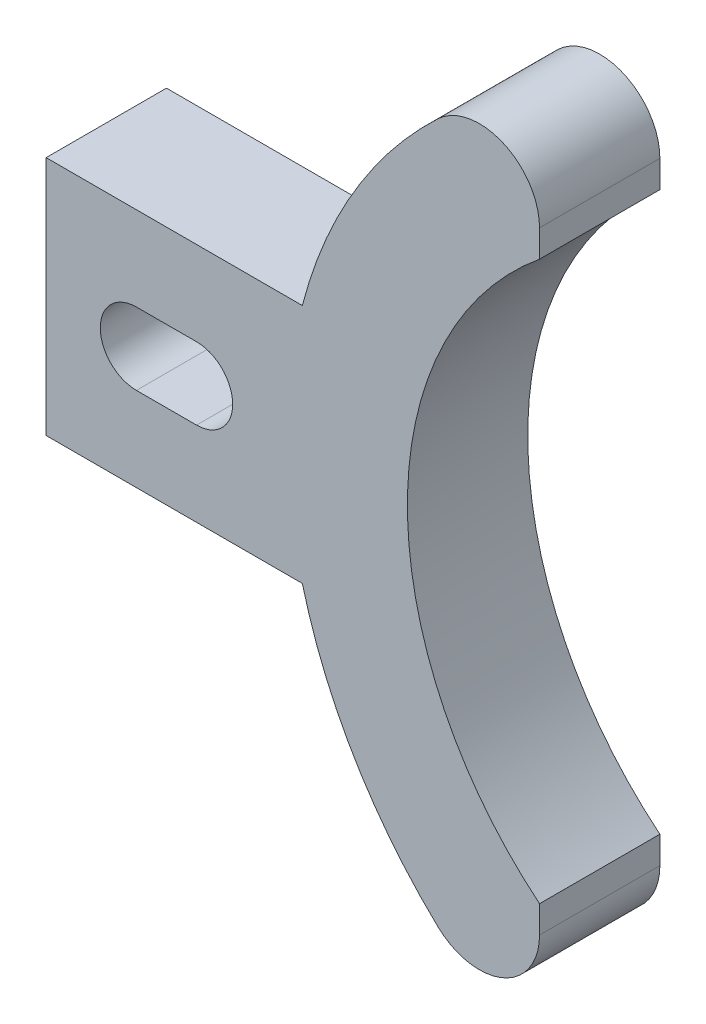
SolidWorks part; units mm, degrees
ref_plane "Front Plane" through (0, 0, 0) normal (0, 0, 1) x (1, 0, 0)
ref_plane "Top Plane" through (0, 0, 0) normal (0, 1, 0) x (1, 0, 0)
ref_plane "Right Plane" through (0, 0, 0) normal (1, 0, 0) x (0, 0, -1)
sketch "Sketch1" plane through (0, 0, 0) normal (0, 0, 1) x (1, 0, 0)
  line L0 (0, 12.7) -> (76.2, 12.7) construction
  line L1 (0, 0) -> (76.2, 0)
  line L2 (0, 0) -> (0, 25.4)
  line L3 (0, 25.4) -> (76.2, 25.4)
  line L4 (76.2, 0) -> (76.2, 25.4)
  line L5 (76.2, 63.475) -> (76.2, -38.075)
  line L6 (25.4, 25.4) -> (25.4, 0) construction
  line L7 (76.2, -38.075) -> (69.85, -38.075)
  line L8 (69.85, -38.075) -> (69.85, 63.475)
  line L9 (69.85, 63.475) -> (76.2, 63.475)
  circle A0 centre (12.7, 12.7) radius 3.81
  circle A1 centre (76.2, 12.7) radius 38.075
  circle A2 centre (76.2, 12.7) radius 50.775
  dimension "D5" = 7.62
  dimension "D6" = 76.15
  dimension "D7" = 12.7
  dimension "D1" = 25.4
  dimension "D2" = 76.2
  dimension "D3" = 25.4
  dimension "D4" = 12.7
  dimension "D8" = 6.35
extrude "Boss-Extrude1" add sketch "Sketch1" along normal blind 12.7 contours A2 L3 L2 L1 A0 | L3 A2 L1 A1 | L8 A2 L3 A1 | L1 A2 L8 A1
ref_plane "Plane4" through (52.07, 0, 0) normal (1, 0, 0) x (0, 0, -1)
sketch "Sketch5" plane through (52.07, 0, 0) normal (1, 0, 0) x (0, 0, -1)
  line L1 (-49.6644, -75.1847) -> (58.4532, -75.1847)
  line L2 (-49.6644, -75.1847) -> (-49.6644, 77.9103)
  line L3 (-49.6644, 77.9103) -> (58.4532, 77.9103)
  line L4 (58.4532, -75.1847) -> (58.4532, 77.9103)
extrude "Cut-Extrude2" cut sketch "Sketch5" along normal through all
fillet "Fillet1" radius 6.35 2 edges at (52.07, 57.3749, 6.35) (52.07, -31.9749, 6.35)
sketch "Sketch6" plane through (0, 0, 12.7) normal (0, 0, 1) x (1, 0, 0)
  line L0 (9.525, 12.7) -> (15.875, 12.7) construction
  line L1 (9.525, 16.51) -> (15.875, 16.51)
  line L2 (9.525, 8.89) -> (15.875, 8.89)
  arc A0 (9.525, 16.51) -> (9.525, 8.89) centre (9.525, 12.7) ccw
  arc A1 (15.875, 8.89) -> (15.875, 16.51) centre (15.875, 12.7) ccw
  circle A2 centre (12.7, 12.7) radius 3.81 construction
  point P2 (12.7, 12.7)
  dimension "D1" = 6.35
extrude "Cut-Extrude3" cut sketch "Sketch6" against normal through all
hole_wizard "M4 Clearance Hole1" positions "Sketch2" profile "Sketch3" hole size "M4" standard "ANSI Metric"
sketch "Sketch2" plane through (69.85, 0, 0) normal (1, 0, 0) x (0, 0, -1)
  line L0 (-6.35, 63.0764) -> (-6.35, 50.2418) construction
  line L1 (-12.7, 63.0764) -> (0, 63.0764) construction
  line L2 (-12.7, 50.2418) -> (0, 50.2418) construction
  line L3 (-6.35, 50.2418) -> (-6.35, -24.8418) construction
  line L4 (-12.7, -24.8418) -> (0, -24.8418) construction
  line L5 (-6.35, -24.8418) -> (-6.35, -37.6764) construction
  line L6 (-12.7, -37.6764) -> (0, -37.6764) construction
  point P17 (-6.35, 56.6591)
  point P19 (-6.35, -31.2591)
sketch "Sketch3" plane through (69.85, -31.2591, 6.35) normal (0, 1, 0) x (0, 0, -1)
  line L0 (0, 0) -> (0, 69.85)
  line L1 (0, 69.85) -> (2.25, 69.85)
  line L2 (2.25, 69.85) -> (2.25, 0)
  line L5 (2.25, 0) -> (0, 0)
  line L11 (0, -6.35) -> (0, 107.95) construction
  dimension "Thru Hole Dia." = 4.5
  dimension "Thru Hole Depth" = 69.85
sketch "Sketch4" plane through (53.975, 0, 0) normal (1, 0, 0) x (0, 0, -1)
  circle A0 centre (-6.35, 56.6591) radius 2.25 construction
  circle A1 centre (-6.35, -31.2591) radius 2.25 construction
  circle A2 centre (-6.35, 56.6591) radius 2.25
  circle A3 centre (-6.35, -31.2591) radius 2.25
  circle A4 centre (-6.35, -31.2591) radius 4.7625
  circle A5 centre (-6.35, 56.6591) radius 4.7625
  dimension "D1" = 9.525
  dimension "D2" = 9.525
extrude "Cut-Extrude1" cut sketch "Sketch4" against normal blind 12.7 contours A4 | A5
